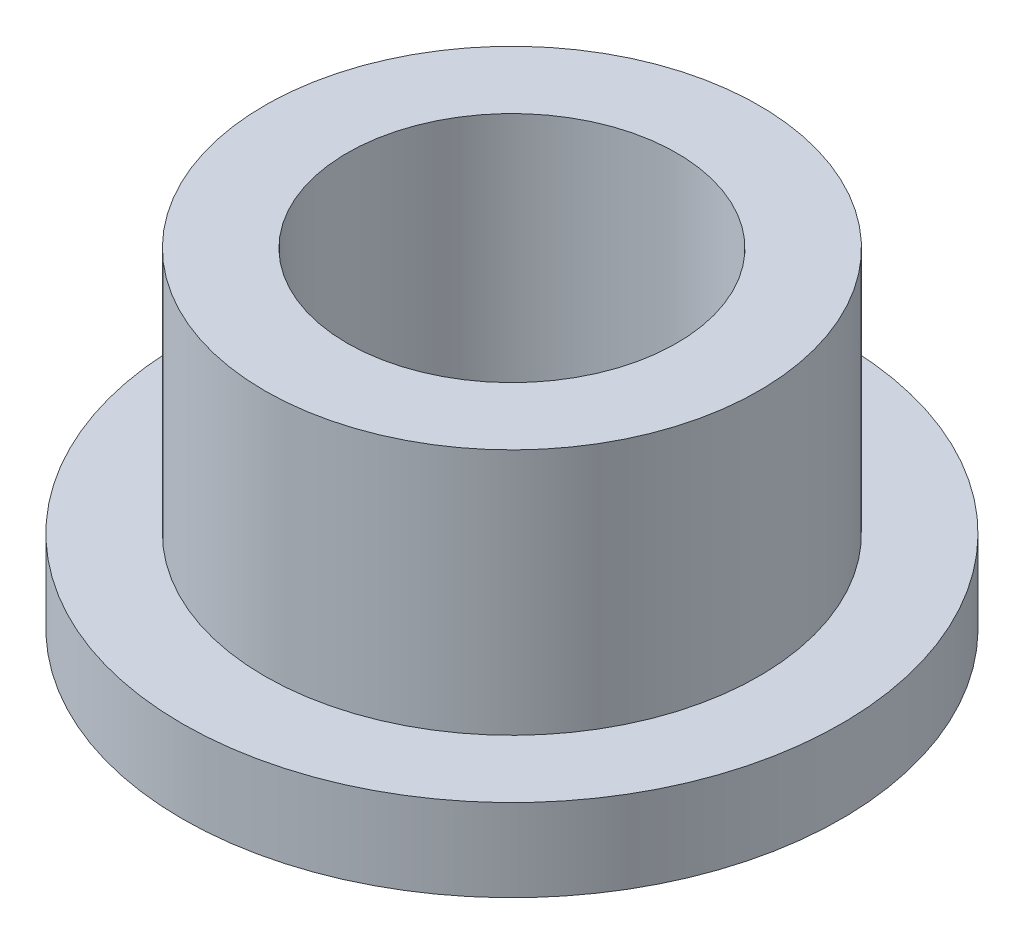
SolidWorks part; units mm, degrees
ref_plane "Front" through (0, 0, 0) normal (0, 0, 1) x (1, 0, 0)
ref_plane "Top" through (0, 0, 0) normal (0, 1, 0) x (1, 0, 0)
ref_plane "Right" through (0, 0, 0) normal (1, 0, 0) x (0, 0, -1)
sketch "Sketch1" plane through (0, 0, 0) normal (0, 1, 0) x (1, 0, 0)
  circle A0 centre (0, 0) radius 3.175
  circle A1 centre (0, 0) radius 4.7625
  circle A2 centre (0, 0) radius 6.35
  dimension "ID" = 6.35
  dimension "OD" = 9.525
  dimension "FlangeOD" = 12.7
sketch "Sketch2" plane through (0, 0, 0) normal (0, 1, 0) x (1, 0, 0)
  circle A0 centre (0, 0) radius 3.175 construction
  circle A1 centre (0, 0) radius 4.7625 construction
  circle A2 centre (0, 0) radius 3.175
  circle A3 centre (0, 0) radius 4.7625
extrude "Boss-Extrude1" add sketch "Sketch2" along normal blind 6.35
sketch "Sketch3" plane through (0, 0, 0) normal (0, 1, 0) x (1, 0, 0)
  circle A0 centre (0, 0) radius 6.35 construction
  circle A1 centre (0, 0) radius 4.7625 construction
  circle A2 centre (0, 0) radius 6.35
  circle A3 centre (0, 0) radius 4.7625
extrude "Boss-Extrude2" add sketch "Sketch3" along normal blind 1.5875
